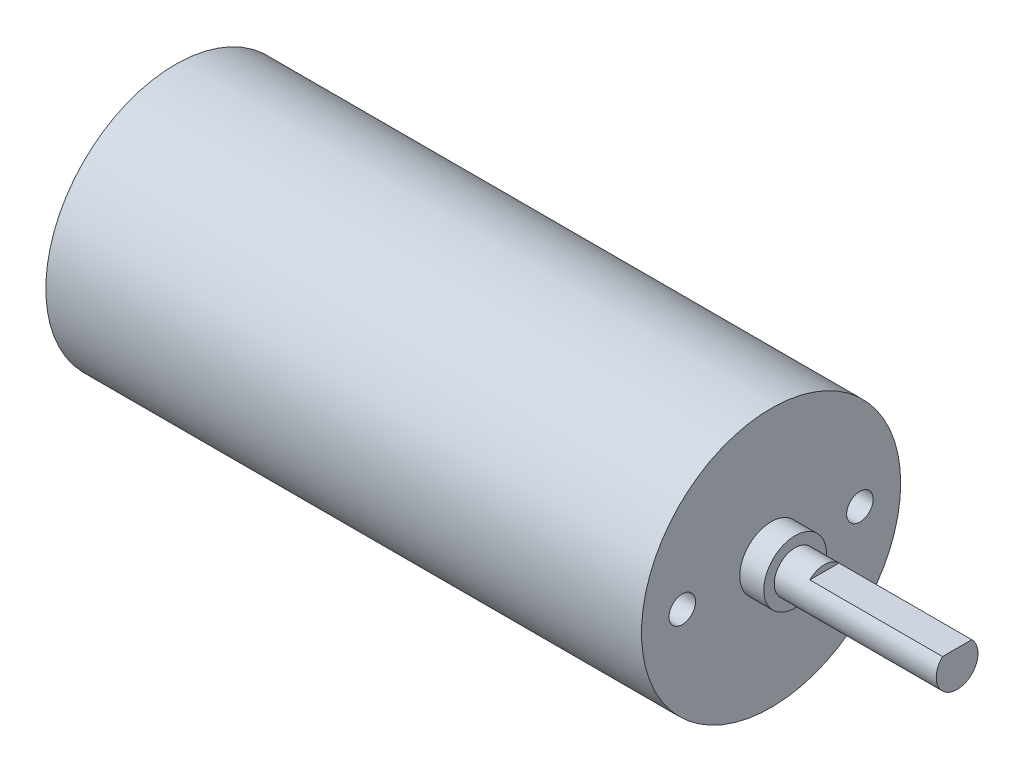
SolidWorks part; units mm, degrees
ref_plane "Front Plane" through (0, 0, 0) normal (0, 0, 1) x (1, 0, 0)
ref_plane "Top Plane" through (0, 0, 0) normal (0, 1, 0) x (1, 0, 0)
ref_plane "Right Plane" through (0, 0, 0) normal (1, 0, 0) x (0, 0, -1)
sketch "Sketch1" plane through (0, 0, 0) normal (1, 0, 0) x (0, 0, -1)
  circle A0 centre (0, 0) radius 12.4
  dimension "D1" = 24.8
extrude "Boss-Extrude1" add sketch "Sketch1" against normal blind 57
sketch "Sketch2" plane through (0, 0, 0) normal (1, 0, 0) x (0, 0, -1)
  circle A0 centre (0, 0) radius 3
  dimension "D1" = 6
extrude "Boss-Extrude2" add sketch "Sketch2" along normal blind 2.3
sketch "Sketch3" plane through (2.3, 0, 0) normal (1, 0, 0) x (0, 0, -1)
  circle A0 centre (0, 0) radius 2
  dimension "D1" = 4
extrude "Boss-Extrude3" add sketch "Sketch3" along normal blind 15.5
sketch "Sketch4" plane through (0, 0, 0) normal (1, 0, 0) x (0, 0, -1)
  line L0 (-8.5, 0) -> (8.5, 0) construction
  line L1 (0, 0) -> (-8.5, 0) construction
  circle A0 centre (8.5, 0) radius 1.27
  circle A1 centre (-8.5, 0) radius 1.27
  dimension "D3" = 2.54
  dimension "D4" = 2.54
  dimension "D1" = 8.5
  dimension "D2" = 17
extrude "Cut-Extrude1" cut sketch "Sketch4" against normal blind 5
sketch "Sketch5" plane through (17.8, 0, 0) normal (1, 0, 0) x (0, 0, -1)
  line L0 (0, -2) -> (0, 1.429) construction
  line L1 (0, 1.429) -> (-1.3993, 1.429)
  line L2 (0, 1.429) -> (1.3993, 1.429)
  circle A0 centre (0, 0) radius 2 construction
  arc A1 (-1.3993, 1.429) -> (1.3993, 1.429) centre (0, 0) cw
  dimension "D1" = 3.429
extrude "Cut-Extrude3" cut sketch "Sketch5" against normal blind 12.7
